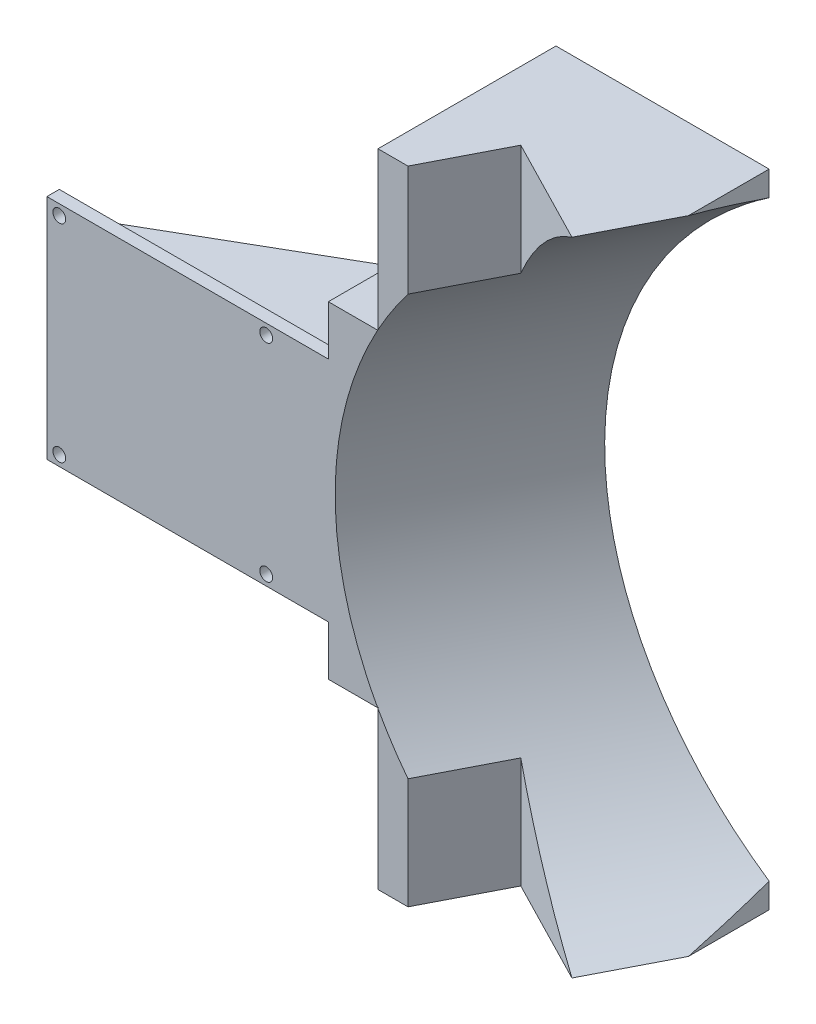
SolidWorks part; units mm, degrees
material "PTFE(普通)"
ref_plane "前视基准面" through (0, 0, 0) normal (0, 0, 1) x (1, 0, 0)
ref_plane "上视基准面" through (0, 0, 0) normal (0, 1, 0) x (1, 0, 0)
ref_plane "右视基准面" through (0, 0, 0) normal (1, 0, 0) x (0, 0, -1)
other "Configuration Table"
sketch "草图1" plane through (0, 0, 0) normal (0, 0, 1) x (1, 0, 0)
  line L1 (40, -27.5) -> (-40, -27.5)
  line L2 (40, -27.5) -> (40, 27.5)
  line L3 (40, 27.5) -> (-40, 27.5)
  line L4 (-40, -27.5) -> (-40, 27.5)
  line L5 (40, -27.5) -> (-40, 27.5) construction
  line L6 (40, 27.5) -> (-40, -27.5) construction
  point P0 (0, 0)
  dimension "D1" = 40
  dimension "D2" = 27.5
extrude "凸台-拉伸1" add sketch "草图1" along normal blind 3
sketch "草图2" plane through (0, 0, 0) normal (0, 0, -1) x (-1, 0, 0)
  line L0 (-40, 27.5) -> (40, 27.5) construction
  line L1 (40, -27.5) -> (-40, -27.5) construction
  line L2 (40, 27.5) -> (40, -27.5) construction
  line L3 (37, 25) -> (37, -25) construction
  circle A0 centre (37, 25) radius 1.55
  circle A1 centre (37, -25) radius 1.55
  circle A2 centre (-13, 25) radius 1.55
  circle A3 centre (-13, -25) radius 1.55
  dimension "D1" = 3.1
  dimension "D2" = 3.1
  dimension "D3" = 3.1
  dimension "D4" = 3.1
  dimension "D5" = 2.5
  dimension "D6" = 2.5
  dimension "D7" = 3
  dimension "D8" = 50
  dimension "D9" = 50
extrude "切除-拉伸1" cut sketch "草图2" against normal blind 24.5 contours A3 | A1 | A0 | A2
sketch "草图3" plane through (40, 0, 0) normal (1, 0, 0) x (0, 0, -1)
  line L1 (-3, 27.5) -> (0, 27.5)
  line L2 (-3, 27.5) -> (-3, -27.5)
  line L3 (-3, -27.5) -> (0, -27.5)
  line L4 (0, 27.5) -> (0, -27.5)
extrude "凸台-拉伸2" add sketch "草图3" along normal blind 1.5 separate body
sketch "草图4" plane through (0, 0, 3) normal (0, 0, 1) x (1, 0, 0)
  line L0 (40, 0) -> (41.5, 0) construction
  line L1 (40, -27.5) -> (40, 27.5) construction
  line L2 (41.5, 27.5) -> (41.5, -27.5) construction
sketch "草图5" plane through (41.5, 0, 0) normal (1, 0, 0) x (0, 0, -1)
  line L1 (-3, 27.5) -> (0, 27.5)
  line L2 (-3, 27.5) -> (-3, -27.5)
  line L3 (-3, -27.5) -> (0, -27.5)
  line L4 (0, 27.5) -> (0, -27.5)
extrude "凸台-拉伸3" add sketch "草图5" along normal blind 50
sketch "草图6" plane through (0, 27.5, 0) normal (0, 1, 0) x (1, 0, 0)
  line L1 (40, 0) -> (91.5, 0)
  line L2 (40, 0) -> (40, -3)
  line L3 (40, -3) -> (91.5, -3)
  line L4 (91.5, 0) -> (91.5, -3)
extrude "凸台-拉伸4" add sketch "草图6" along normal blind 50
sketch "草图7" plane through (0, -27.5, 0) normal (0, -1, 0) x (1, 0, 0)
  line L0 (40, 3) -> (41.5, 3) construction
  line L1 (40, 3) -> (91.5, 3)
  line L2 (40, 3) -> (40, 0)
  line L3 (40, 0) -> (91.5, 0)
  line L4 (91.5, 3) -> (91.5, 0)
  line L5 (-40, 3) -> (91.5, 3) construction
extrude "凸台-拉伸5" add sketch "草图7" along normal blind 50
sketch "草图8" plane through (0, 0, 0) normal (0, 0, -1) x (-1, 0, 0)
  line L1 (-91.5, 77.5) -> (-40, 77.5)
  line L2 (-91.5, 77.5) -> (-91.5, -77.5)
  line L3 (-91.5, -77.5) -> (-40, -77.5)
  line L4 (-40, 77.5) -> (-40, -77.5)
extrude "凸台-拉伸6" add sketch "草图8" along normal blind 40
sketch "草图9" plane through (40, 0, 0) normal (-1, 0, 0) x (0, 0, 1)
  line L0 (-40, 39.5) -> (3, 39.5)
  line L1 (-40, -77.5) -> (-40, 77.5) construction
  line L2 (3, 77.5) -> (3, 27.5) construction
  line L3 (-40, -39.5) -> (3, -39.5)
  line L4 (3, -77.5) -> (3, -27.5) construction
  line L5 (-40, 77.5) -> (3, 77.5) construction
  line L6 (3, -77.5) -> (-40, -77.5) construction
  line L7 (-40, 39.5) -> (-40, -39.5)
  line L8 (3, 39.5) -> (3, 27.5)
  line L9 (3, 27.5) -> (0, 27.5)
  line L10 (0, 27.5) -> (0, -27.5)
  line L11 (0, -27.5) -> (3, -27.5)
  line L12 (3, -27.5) -> (3, -39.5)
  dimension "D1" = 38
  dimension "D2" = 38
extrude "凸台-拉伸7" add sketch "草图9" along normal blind 12
sketch "草图10" plane through (0, 77.5, 0) normal (0, 1, 0) x (1, 0, 0)
  line L0 (40, -3) -> (91.5, -3) construction
  line L2 (91.5, -3) -> (91.5, 40) construction
  line L3 (56.5, 15) -> (91.5, -3)
  line L4 (56.5, 15) -> (47.2429, -3)
  line L5 (47.2429, -3) -> (91.5, -3)
  point P0 (56.5, 15)
  point P5 (56.5, 12)
  dimension "D1" = 18
  dimension "D2" = 35
sketch "草图11" plane through (0, -77.5, 0) normal (0, -1, 0) x (1, 0, 0)
  line L0 (91.5, 3) -> (56.5, -15)
extrude "切除-拉伸2" cut sketch "草图10" against normal blind 184 contours L4 L5 L3
sketch "草图13" plane through (17.9187, 0, -34.8418) normal (-0.4573, 0, 0.8893) x (0.8893, 0, 0.4573)
  line L0 (82.7419, 77.5) -> (82.7419, -77.5) construction
  line L1 (82.7419, -77.5) -> (43.3845, -77.5) construction
  circle A0 centre (117.7419, 0) radius 90
  dimension "D1" = 35
  dimension "D2" = 180
  dimension "D3" = 77.5
extrude "切除-拉伸3" cut sketch "草图13" along normal mid plane 184
sketch "草图14" plane through (0, 0, 0) normal (0, 0, -1) x (-1, 0, 0)
  line L0 (40, 27.5) -> (40, -27.5) construction
  line L1 (40, 18.5) -> (-28, 18.5)
  line L2 (40, 18.5) -> (40, -18.5)
  line L3 (40, -18.5) -> (-28, -18.5)
  line L4 (-28, 18.5) -> (-28, -18.5)
  line L5 (-28, 39.5) -> (-28, -39.5) construction
  line L6 (-28, 27.5) -> (40, 27.5) construction
  line L7 (40, -27.5) -> (-28, -27.5) construction
  dimension "D1" = 9
  dimension "D2" = 9
sketch "草图15" plane through (28, 0, 0) normal (-1, 0, 0) x (0, 0, 1)
  line L2 (-40, 39.5) -> (-40, -39.5)
  line L3 (0, 18.5) -> (0, -18.5) construction
  dimension "D1" = 40
extrude "凸台-拉伸8" add sketch "草图14" along normal blind 40
sketch "草图16" plane through (0, 18.5, 0) normal (0, 1, 0) x (1, 0, 0)
  line L0 (-40, 5.8486) -> (19.2102, 40)
  line L1 (-40, 40) -> (-40, 0) construction
  line L2 (-40, 40) -> (28, 40) construction
  line L3 (19.2102, 40) -> (-40, 40)
  line L4 (-40, 40) -> (-40, 5.8486)
  dimension "D1" = 59.2102
  dimension "D2" = 34.1514
extrude "切除-拉伸4" cut sketch "草图16" against normal blind 56 contours L3 L4 L0
